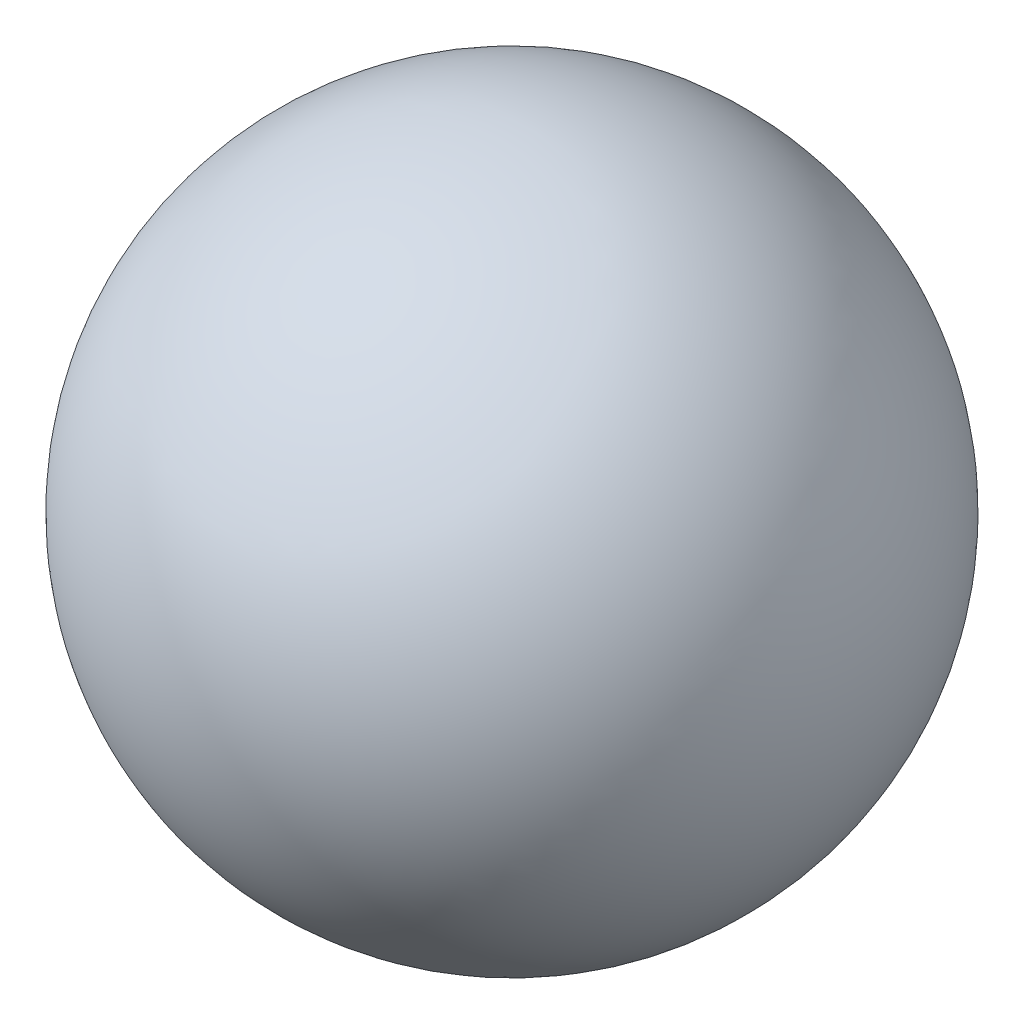
SolidWorks part; units mm, degrees
ref_plane "Plan de face" through (0, 0, 0) normal (0, 0, 1) x (1, 0, 0)
ref_plane "Plan de dessus" through (0, 0, 0) normal (0, 1, 0) x (1, 0, 0)
ref_plane "Plan de droite" through (0, 0, 0) normal (1, 0, 0) x (0, 0, -1)
sketch "Esquisse1" plane through (0, 0, 0) normal (0, 1, 0) x (1, 0, 0)
  line L0 (0, 6) -> (0, -6)
  arc A1 (0, 6) -> (0, -6) centre (0, 0) ccw
revolve "Révolution1" add sketch "Esquisse1" angle 360 about L0
